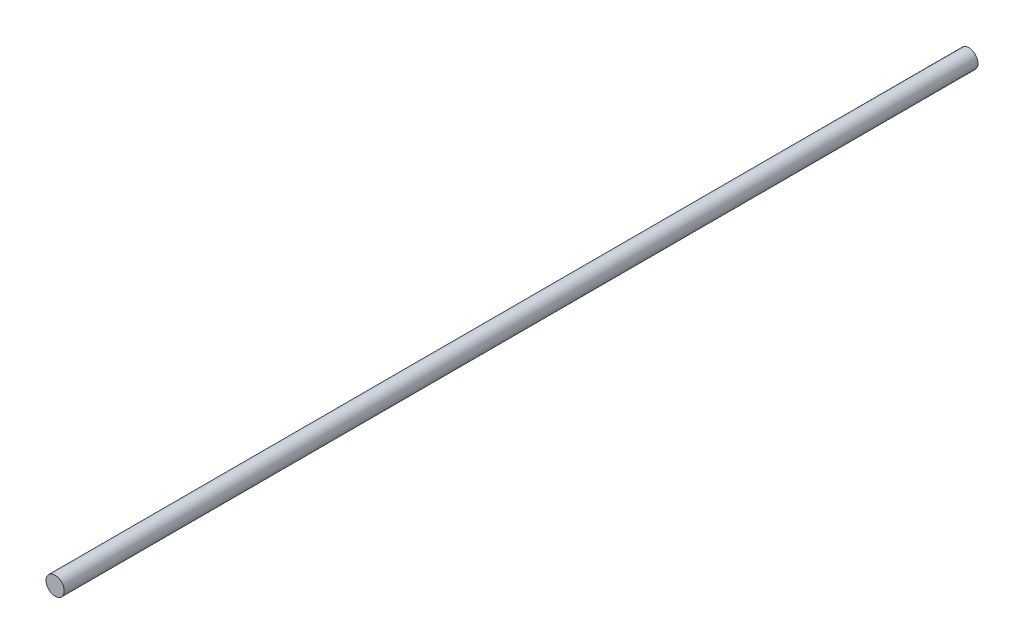
SolidWorks part; units mm, degrees
ref_plane "Front" through (0, 0, 0) normal (0, 0, 1) x (1, 0, 0)
ref_plane "Top" through (0, 0, 0) normal (0, 1, 0) x (1, 0, 0)
ref_plane "Right" through (0, 0, 0) normal (1, 0, 0) x (0, 0, -1)
sketch "Sketch1" plane through (0, 0, 0) normal (0, 0, 1) x (1, 0, 0)
  circle A0 centre (0, 0) radius 4
  dimension "D1" = 8
extrude "rod body" add sketch "Sketch1" along normal blind 400
thread "Thread1" pitch 1.8143 start angle 0, offset 0, length 0, pitch 1.8143, diameter 8
ref_plane "Plane1" through (-4, 0, 400) normal (0, -1, 0) x (-1, 0, 0)
sketch "Thread Profile1" plane through (-4, 0, 400) normal (0, -1, 0) x (-1, 0, 0)
  line L0 (0, 0) -> (0, 1.8143) construction
  line L11 (0, 0) -> (0, 1.5875)
  line L12 (0, 1.5875) -> (-0.982, 1.0205)
  line L13 (-0.982, 1.0205) -> (-0.982, 0.567)
  line L15 (-0.982, 0.567) -> (0, 0)
  line L17 (-0.982, 0.7937) -> (0, 0.7937) construction
  point P2 (0, 0)
  dimension "Pitch" = 1.8143
  dimension "Profile_Angle" = 60
  dimension "Profile_Land" = 0.4536
  dimension "Profile_Height" = 0.982
